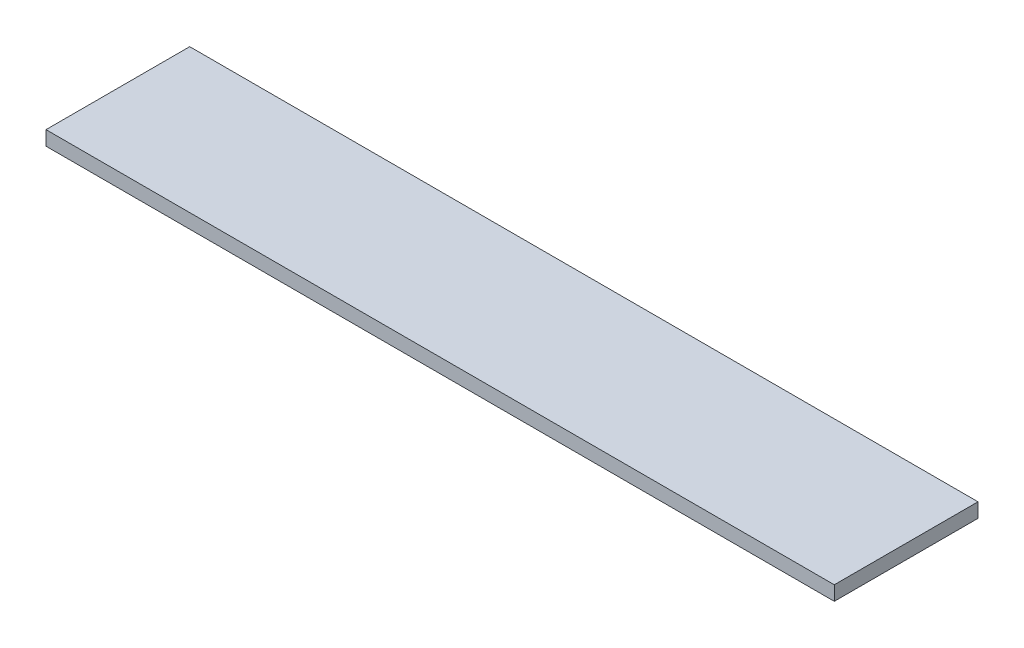
SolidWorks part; units mm, degrees
ref_plane "Front Plane" through (0, 0, 0) normal (0, 0, 1) x (1, 0, 0)
ref_plane "Top Plane" through (0, 0, 0) normal (0, 1, 0) x (1, 0, 0)
ref_plane "Right Plane" through (0, 0, 0) normal (1, 0, 0) x (0, 0, -1)
sketch "Sketch1" plane through (0, 0, 0) normal (0, 1, 0) x (1, 0, 0)
  line L0 (-274.265, 50) -> (274.265, -50) construction
  line L1 (-274.265, 50) -> (274.265, 50)
  line L2 (-274.265, 50) -> (-274.265, -50)
  line L3 (-274.265, -50) -> (274.265, -50)
  line L4 (274.265, 50) -> (274.265, -50)
  dimension "D1" = 548.53
  dimension "D2" = 100
extrude "Boss-Extrude1" add sketch "Sketch1" along normal blind 10
